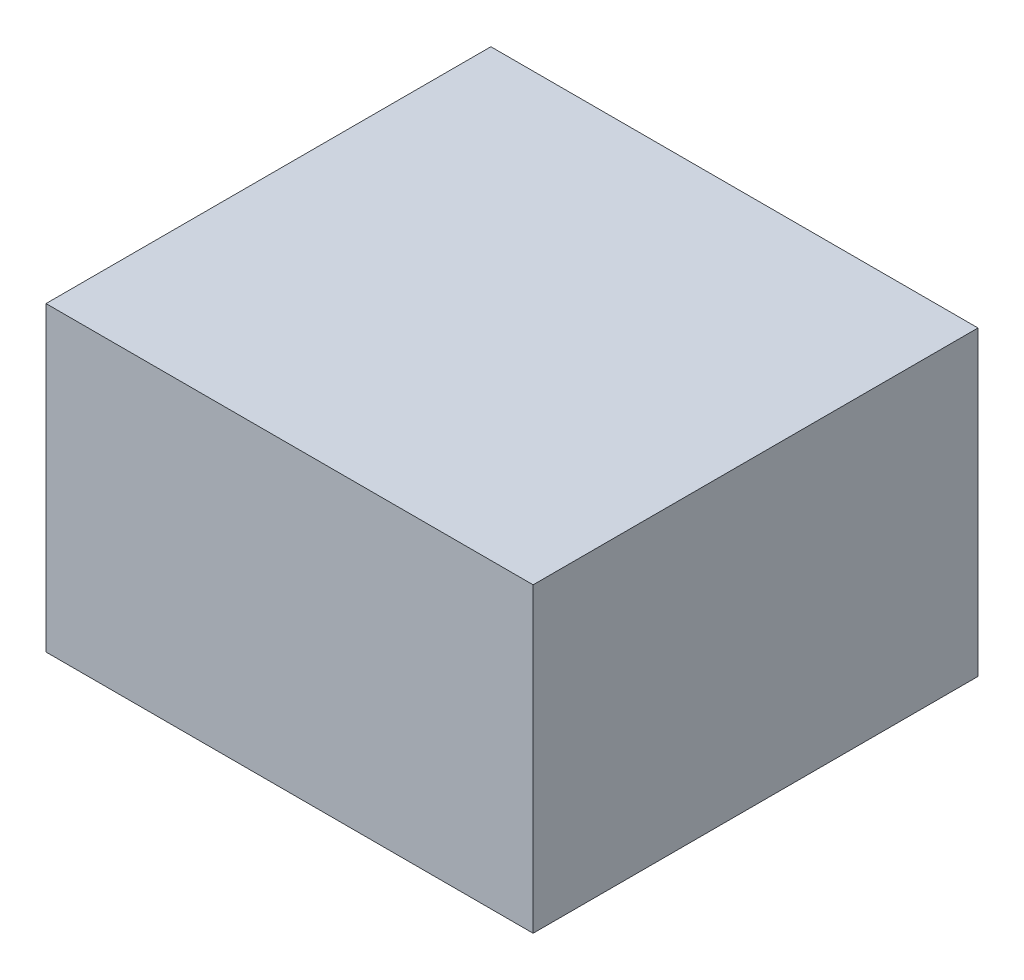
SolidWorks part; units mm, degrees
ref_plane "Front Plane" through (0, 0, 0) normal (0, 0, 1) x (1, 0, 0)
ref_plane "Top Plane" through (0, 0, 0) normal (0, 1, 0) x (1, 0, 0)
ref_plane "Right Plane" through (0, 0, 0) normal (1, 0, 0) x (0, 0, -1)
sketch "Sketch1" plane through (0, 0, 0) normal (0, 0, 1) x (1, 0, 0)
  line L1 (-43.7995, 27.135) -> (43.7995, 27.135)
  line L2 (-43.7995, 27.135) -> (-43.7995, -27.135)
  line L3 (-43.7995, -27.135) -> (43.7995, -27.135)
  line L4 (43.7995, 27.135) -> (43.7995, -27.135)
  line L5 (-43.7995, 27.135) -> (43.7995, -27.135) construction
  line L6 (-43.7995, -27.135) -> (43.7995, 27.135) construction
  point P0 (0, 0)
extrude "Boss-Extrude1" add sketch "Sketch1" along normal blind 80
